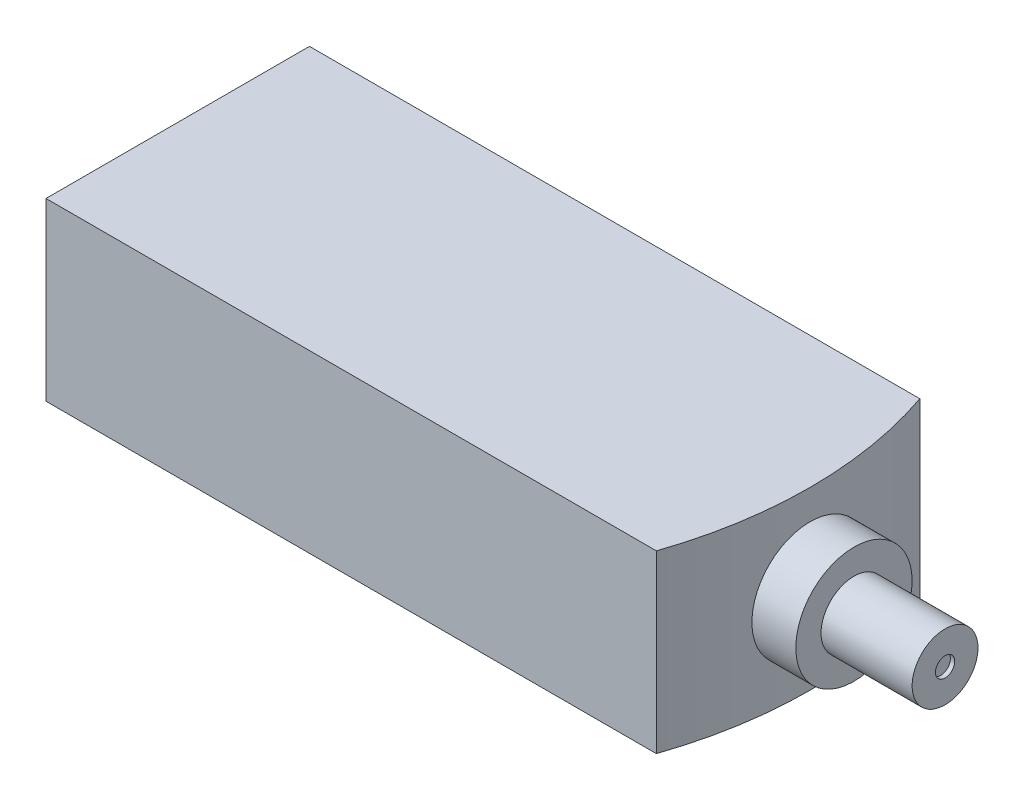
SolidWorks part; units mm, degrees
ref_plane "Front Plane" through (0, 0, 0) normal (0, 0, 1) x (1, 0, 0)
ref_plane "Top Plane" through (0, 0, 0) normal (0, 1, 0) x (1, 0, 0)
ref_plane "Right Plane" through (0, 0, 0) normal (1, 0, 0) x (0, 0, -1)
sketch "Sketch1" plane through (0, 0, 0) normal (0, 1, 0) x (1, 0, 0)
  line L1 (-254.3353, 102.4282) -> (95.1647, 102.4282)
  line L2 (-254.3353, 102.4282) -> (-254.3353, -17.5718)
  line L3 (-254.3353, -17.5718) -> (95.1647, -17.5718)
  line L4 (95.1647, 102.4282) -> (95.1647, -17.5718)
  dimension "D1" = 349.5
  dimension "D2" = 120
extrude "Boss-Extrude1" add sketch "Sketch1" along normal blind 80
sketch "Sketch2" plane through (0, 80, 0) normal (0, 1, 0) x (1, 0, 0)
  line L0 (95.1647, 102.4282) -> (53.6647, 102.4282)
  line L3 (95.1647, 102.4282) -> (-254.3353, 102.4282) construction
  line L4 (53.6647, 102.4282) -> (53.6647, -17.5718)
  line L5 (-254.3353, -17.5718) -> (95.1647, -17.5718) construction
  line L6 (53.6647, -17.5718) -> (95.1647, -17.5718)
  line L7 (95.1647, -17.5718) -> (95.1647, 102.4282)
  dimension "D1" = 41.5
extrude "Cut-Extrude1" cut sketch "Sketch2" against normal through all
sketch "Sketch3" plane through (0, 80, 0) normal (0, 1, 0) x (1, 0, 0)
  line L0 (53.6647, 102.4282) -> (23.6647, 102.4282)
  line L1 (53.6647, 102.4282) -> (-254.3353, 102.4282) construction
  line L2 (53.6647, -17.5718) -> (23.6647, -17.5718)
  line L3 (-254.3353, -17.5718) -> (53.6647, -17.5718) construction
  line L7 (53.6647, 102.4282) -> (53.6647, -17.5718)
  arc A0 (23.6647, -17.5718) -> (23.6647, 102.4282) centre (-151.3353, 42.4282) ccw
  dimension "D1" = 30
  dimension "D2" = 30
extrude "Cut-Extrude4" cut sketch "Sketch3" against normal blind 80 contours A0 L0 L7 L2
ref_plane "Plane1" through (33.6647, 0, 0) normal (1, 0, 0) x (0, 0, -1)
sketch "Sketch4" plane through (33.6647, 0, 0) normal (1, 0, 0) x (0, 0, -1)
  line L0 (102.4282, 80) -> (-17.5718, 80) construction
  line L1 (102.4282, 0) -> (102.4282, 80) construction
  circle A0 centre (42.4282, 40) radius 26.4829
  point P6 (102.4282, 40)
  dimension "D1" = 40
  dimension "D2" = 60
extrude "Boss-Extrude2" add sketch "Sketch4" along normal blind 20 separate body
sketch "Sketch5" plane through (53.6647, 0, 0) normal (1, 0, 0) x (0, 0, -1)
  circle A0 centre (42.4282, 40) radius 15
  circle A1 centre (42.4282, 40) radius 26.4829 construction
  dimension "D1" = 30
extrude "Boss-Extrude3" add sketch "Sketch5" along normal blind 41.5
sketch "Sketch6" plane through (-254.3353, 0, 0) normal (-1, 0, 0) x (0, 0, 1)
  circle A0 centre (-70.8071, 44.6897) radius 7.5
  dimension "D1" = 15
extrude "Boss-Extrude4" add sketch "Sketch6" along normal blind 8.5
sketch "Sketch7" plane through (0, 0, 0) normal (0, -1, 0) x (1, 0, 0)
  line L0 (-254.3353, -102.4282) -> (-254.3353, 17.5718) construction
  line L1 (-254.3353, 17.5718) -> (23.6647, 17.5718) construction
  circle A0 centre (-142.3353, -42.4282) radius 3
  circle A1 centre (-57.3353, -42.4282) radius 3
  circle A2 centre (-129.8353, -42.4282) radius 2
  circle A3 centre (-69.8353, -42.4282) radius 2
  point P4 (-254.3353, -42.4282)
  point P15 (-139.3353, -42.4282)
  dimension "D2" = 6
  dimension "D4" = 6
  dimension "D6" = 4
  dimension "D7" = 4
  dimension "D1" = 112
  dimension "D3" = 60
  dimension "D5" = 85
  dimension "D8" = 60
  dimension "D9" = 12.5
extrude "Cut-Extrude5" cut sketch "Sketch7" against normal blind 10
sketch "Sketch8" plane through (95.1647, 0, 0) normal (1, 0, 0) x (0, 0, -1)
  circle A0 centre (42.4282, 40) radius 4.4058
  circle A1 centre (42.4282, 40) radius 15 construction
extrude "Cut-Extrude6" cut sketch "Sketch8" against normal blind 2
